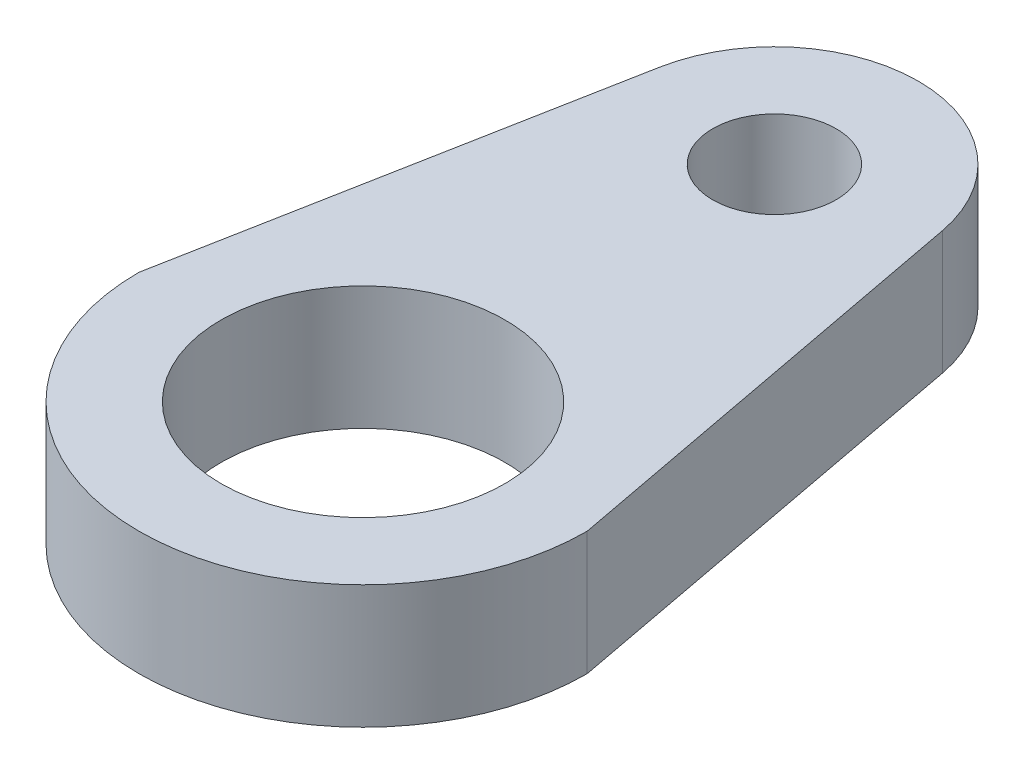
SolidWorks part; units mm, degrees
ref_plane "Plano frontal" through (0, 0, 0) normal (0, 0, 1) x (1, 0, 0)
ref_plane "Plano superior" through (0, 0, 0) normal (0, 1, 0) x (1, 0, 0)
ref_plane "Plano direito" through (0, 0, 0) normal (1, 0, 0) x (0, 0, -1)
sketch "Sketch1" plane through (0, 0, 0) normal (0, 1, 0) x (1, 0, 0)
  line L0 (-5.45, 0) -> (-3.4392, 10.6494)
  line L1 (5.45, 0) -> (3.4392, 10.6494)
  circle A0 centre (0, 0) radius 13.5 construction
  circle A1 centre (0, 0) radius 3.45
  circle A2 centre (0, 10) radius 1.5
  circle A3 centre (0, 10) radius 3 construction
  arc A4 (3.4392, 10.6494) -> (-3.4392, 10.6494) centre (0, 10) ccw
  arc A5 (-5.45, 0) -> (5.45, 0) centre (0, 0) ccw
  circle A7 centre (0, 0) radius 5.45 construction
  circle A8 centre (0, 10) radius 3.5 construction
  point P13 (5.2119, 1.5934)
  point P15 (3.3471, 11.0233)
  dimension "D1" = 10
  dimension "D2" = 6.9
  dimension "D3" = 3
  dimension "D4" = 2
  dimension "D5" = 27
  dimension "D6" = 5.05
  dimension "D7" = 6
  dimension "D8" = 3.55
  dimension "D9" = 2
  dimension "D10" = 2
extrude "Boss-Extrude1" add sketch "Sketch1" along normal mid plane 3
